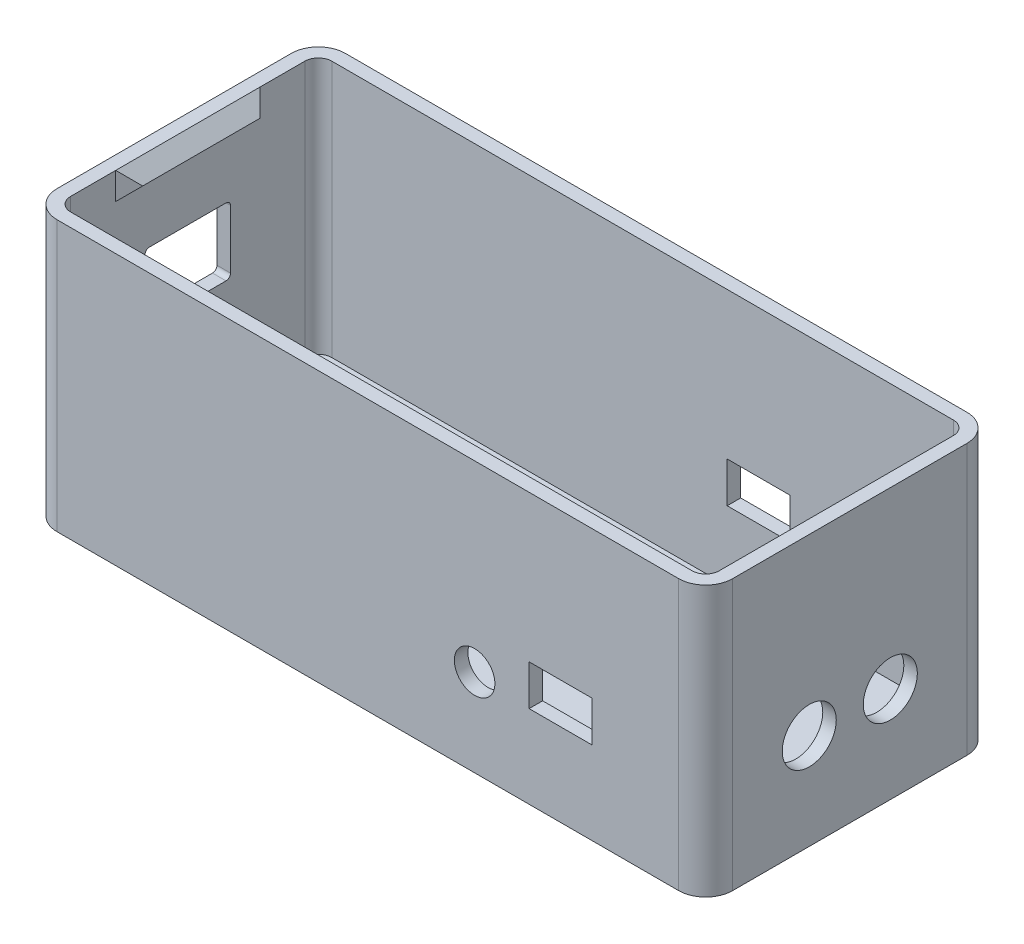
SolidWorks part; units mm, degrees
ref_plane "Front Plane" through (0, 0, 0) normal (0, 0, 1) x (1, 0, 0)
ref_plane "Top Plane" through (0, 0, 0) normal (0, 1, 0) x (1, 0, 0)
ref_plane "Right Plane" through (0, 0, 0) normal (1, 0, 0) x (0, 0, -1)
sketch "Sketch1" plane through (0, 0, 0) normal (0, 1, 0) x (1, 0, 0)
  line L1 (-37.5, -16) -> (37.5, -16)
  line L2 (-37.5, -16) -> (-37.5, 16)
  line L3 (-37.5, 16) -> (37.5, 16)
  line L4 (37.5, -16) -> (37.5, 16)
  line L5 (-37.5, -16) -> (37.5, 16) construction
  line L6 (-37.5, 16) -> (37.5, -16) construction
  point P0 (0, 0)
  dimension "D1" = 75
  dimension "D2" = 32
extrude "Boss-Extrude1" add sketch "Sketch1" along normal blind 30
fillet "Fillet1" radius 3 4 edges at (-37.5, 15, -16) (37.5, 15, -16) (-37.5, 15, 16) (37.5, 15, 16)
shell "Shell1" thickness 1.5
sketch "Sketch2" plane through (36, 0, 0) normal (-1, 0, 0) x (0, 0, 1)
  line L0 (13, 30) -> (-13, 30) construction
  line L1 (-8, 30) -> (8, 30)
  line L2 (-8, 30) -> (-8, 27)
  line L3 (-8, 27) -> (8, 27)
  line L4 (8, 30) -> (8, 27)
  line L5 (0, 30.7418) -> (0, 19.9106) construction
  dimension "D2" = 16
extrude "Boss-Extrude2" add sketch "Sketch2" along normal through all draft 45
mirror "Mirror1" about plane through (0, 0, 0) normal (1, 0, 0) of "Boss-Extrude2"
sketch "Sketch3" plane through (37.5, 0, 0) normal (1, 0, 0) x (0, 0, -1)
  line L0 (0, 30.8234) -> (0, -2.2108) construction
  line L1 (-13, 0) -> (13, 0) construction
  circle A0 centre (-4.5, 10.65) radius 3
  circle A1 centre (4.5, 10.65) radius 3
  dimension "D1" = 6
  dimension "D2" = 10.65
  dimension "D3" = 9
extrude "Cut-Extrude1" cut sketch "Sketch3" against normal up to next
sketch "Sketch5" plane through (-37.5, 0, 0) normal (-1, 0, 0) x (0, 0, 1)
  line L0 (-16, 19.25) -> (16, 19.25) construction
  line L1 (-16, 0) -> (-16, 30) construction
  line L2 (16, 30) -> (16, 0) construction
  line L3 (-13, 30) -> (13, 30) construction
  line L4 (0, 30) -> (0, 0) construction
  line L5 (4.75, 13.25) -> (-4.75, 13.25)
  line L6 (4.75, 13.25) -> (4.75, 20.75)
  line L7 (4.75, 20.75) -> (-4.75, 20.75)
  line L8 (-4.75, 13.25) -> (-4.75, 20.75)
  line L9 (4.75, 13.25) -> (-4.75, 20.75) construction
  line L10 (4.75, 20.75) -> (-4.75, 13.25) construction
  point P8 (0, 17)
  dimension "D1" = 10.75
  dimension "D2" = 1.5
  dimension "D3" = 7.5
  dimension "D4" = 9.5
extrude "Cut-Extrude2" cut sketch "Sketch5" against normal up to next
sketch "Sketch6" plane through (0, 0, 0) normal (0, -1, 0) x (1, 0, 0)
  line L0 (0, 16) -> (0, -16) construction
  line L1 (-34.5, 16) -> (34.5, 16) construction
  line L2 (34.5, -16) -> (-34.5, -16) construction
  line L3 (37.5, 13) -> (37.5, -13) construction
  line L4 (37.5, 0) -> (-37.5, 0) construction
  line L5 (0, 13) -> (-16, 13)
  line L6 (0, 13) -> (0, -13)
  line L7 (0, -13) -> (-16, -13)
  line L8 (-16, 13) -> (-16, -13)
  line L9 (-37.5, -13) -> (-37.5, 13) construction
  dimension "D1" = 37.5
  dimension "D2" = 16
  dimension "D3" = 26
extrude "Cut-Extrude3" cut sketch "Sketch6" against normal up to next
fillet "Fillet2" radius 0.5 4 edges at (0, 0.75, -13) (-16, 0.75, -13) (0, 0.75, 13) (-16, 0.75, 13)
fillet "Fillet3" radius 0.5 4 edges at (-36.75, 13.25, -4.75) (-36.75, 20.75, -4.75) (-36.75, 13.25, 4.75) (-36.75, 20.75, 4.75)
sketch "Sketch7" plane through (0, 0, -16) normal (0, 0, -1) x (-1, 0, 0)
  line L1 (-9.39, 9.2) -> (-16.39, 9.2)
  line L2 (-9.39, 9.2) -> (-9.39, 13.7)
  line L3 (-9.39, 13.7) -> (-16.39, 13.7)
  line L4 (-16.39, 9.2) -> (-16.39, 13.7)
  line L5 (-12.89, 13.7) -> (-12.89, 9.2) construction
  line L7 (-34.5, 30) -> (34.5, 30) construction
  line L8 (-37.5, 0) -> (-37.5, 30) construction
  dimension "D1" = 16.3
  dimension "D2" = 24.61
  dimension "D3" = 4.5
  dimension "D4" = 7
extrude "Cut-Extrude4" cut sketch "Sketch7" against normal up to next
sketch "Sketch8" plane through (0, 0, 16) normal (0, 0, 1) x (1, 0, 0)
  line L0 (21.4, 13.7) -> (21.4, 9.2) construction
  line L1 (24.9, 13.7) -> (17.9, 13.7)
  line L2 (24.9, 13.7) -> (24.9, 9.2)
  line L3 (24.9, 9.2) -> (17.9, 9.2)
  line L4 (17.9, 13.7) -> (17.9, 9.2)
  line L5 (37.5, 30) -> (37.5, 0) construction
  line L6 (-34.5, 30) -> (34.5, 30) construction
  circle A0 centre (11.85, 9.7) radius 2.25
  point P12 (11.85, 10.2451)
  dimension "D5" = 25.65
  dimension "D6" = 4.5
  dimension "D7" = 20.3
  dimension "D1" = 16.1
  dimension "D2" = 7
  dimension "D3" = 4.5
  dimension "D4" = 16.3
extrude "Cut-Extrude5" cut sketch "Sketch8" against normal up to next
sketch "Sketch9" plane through (0, 1.5, 0) normal (0, 1, 0) x (1, 0, 0)
  line L0 (0, -12.5) -> (0, 12.5) construction
  line L1 (0, 5) -> (4.5, 5)
  line L2 (0, 5) -> (0, -5)
  line L3 (0, -5) -> (4.5, -5)
  line L4 (4.5, 5) -> (4.5, -5)
  line L5 (-37.5, 0) -> (37.5, 0) construction
  line L6 (-37.5, 13) -> (-37.5, -13) construction
  line L7 (37.5, -13) -> (37.5, 13) construction
  dimension "D1" = 10
  dimension "D2" = 4.5
extrude "Cut-Extrude6" cut sketch "Sketch9" against normal blind 1
equation "\"width\"= 32mm"
equation "\"length\" = 75mm"
equation "\"height\"= 30mm"
equation "\"shell\"= 1.5mm"
equation "\"gap\"= 0.2mm"
equation "\"D1@Sketch1\"=\"length\""
equation "\"D2@Sketch1\"=\"width\""
equation "\"D1@Boss-Extrude1\"=\"height\""
equation "\"D1@Shell1\"=\"shell\""
equation "\"D1@Sketch2\"=\"shell\"*2"
equation "\"D2@Sketch2\"=\"width\"/2"
